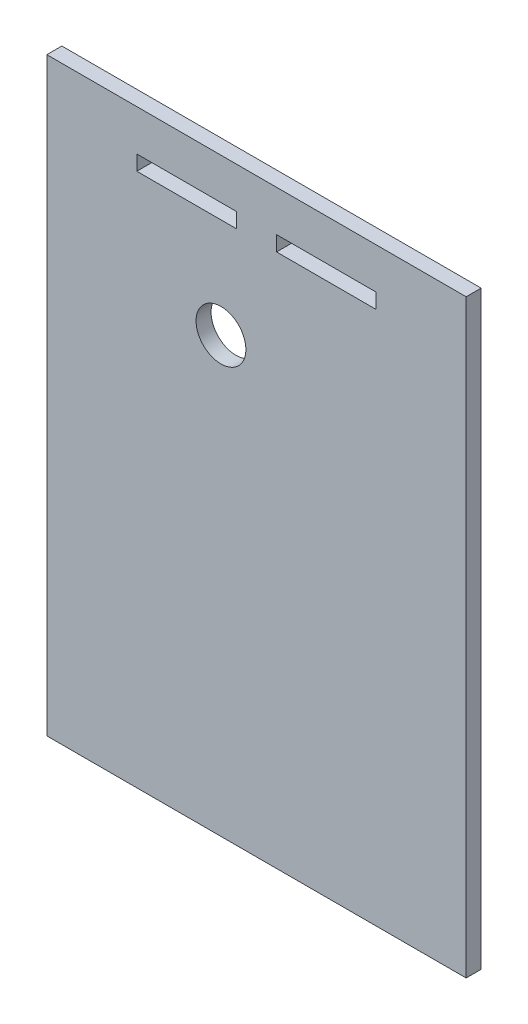
SolidWorks part; units mm, degrees
ref_plane "Alzado" through (0, 0, 0) normal (0, 0, 1) x (1, 0, 0)
ref_plane "Planta" through (0, 0, 0) normal (0, 1, 0) x (1, 0, 0)
ref_plane "Vista lateral" through (0, 0, 0) normal (1, 0, 0) x (0, 0, -1)
sketch "Model" plane through (0, 0, 0) normal (0, 0, 1) x (1, 0, 0)
  line L0 (86.792, -43.8304) -> (2.9253, -43.8304)
  line L1 (86.792, 74.1696) -> (86.792, -43.8304)
  line L2 (2.9253, 74.1696) -> (86.792, 74.1696)
  line L3 (2.9253, 34.4691) -> (2.9253, 74.1696)
  line L4 (2.9253, 34.4691) -> (2.9253, -43.8304)
  line L5 (48.8696, 65.9696) -> (68.8019, 65.9696)
  line L6 (48.8696, 62.9696) -> (48.8696, 65.9696)
  line L7 (68.8019, 62.9696) -> (48.8696, 62.9696)
  line L8 (68.8019, 65.9696) -> (68.8019, 62.9696)
  line L9 (20.9153, 62.9696) -> (20.9153, 65.9696)
  line L10 (40.8477, 62.9696) -> (20.9153, 62.9696)
  line L11 (40.8477, 65.9696) -> (40.8477, 62.9696)
  line L12 (20.9153, 65.9696) -> (40.8477, 65.9696)
  circle A29 centre (37.7504, 42.9905) radius 4.984
extrude "Saliente-Extruir1" add sketch "Model" along normal blind 3
